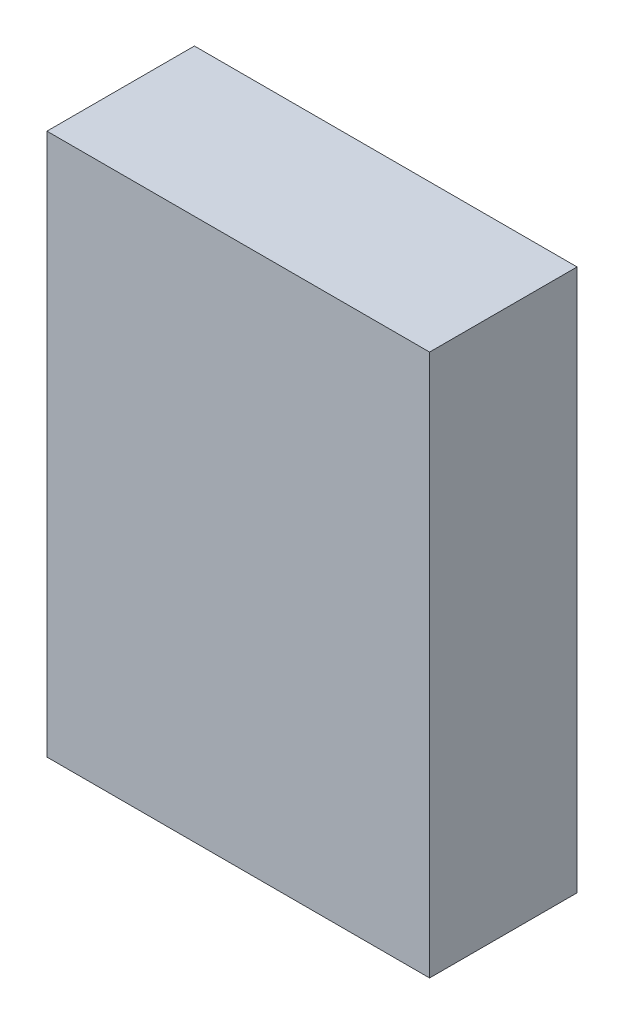
SolidWorks part; units mm, degrees
ref_plane "Plan de face" through (0, 0, 0) normal (0, 0, 1) x (1, 0, 0)
ref_plane "Plan de dessus" through (0, 0, 0) normal (0, 1, 0) x (1, 0, 0)
ref_plane "Plan de droite" through (0, 0, 0) normal (1, 0, 0) x (0, 0, -1)
sketch "Esquisse1" plane through (0, 0, 0) normal (0, 0, 1) x (1, 0, 0)
  line L1 (24, -34) -> (-24, -34)
  line L2 (24, -34) -> (24, 34)
  line L3 (24, 34) -> (-24, 34)
  line L4 (-24, -34) -> (-24, 34)
  line L5 (24, -34) -> (-24, 34) construction
  line L6 (24, 34) -> (-24, -34) construction
  point P0 (0, 0)
  dimension "D1" = 68
  dimension "D2" = 48
extrude "Boss.-Extru.1" add sketch "Esquisse1" along normal blind 18.5
sketch "Esquisse2" plane through (0, 0, 0) normal (0, 0, -1) x (-1, 0, 0)
  line L0 (24, 34) -> (24, -34) construction
  line L1 (18, 31) -> (10, 31)
  line L2 (18, 31) -> (18, 27)
  line L3 (18, 27) -> (10, 27)
  line L4 (10, 31) -> (10, 27)
  line L5 (18, 31) -> (10, 27) construction
  line L6 (18, 27) -> (10, 31) construction
  line L7 (-24, 34) -> (24, 34) construction
  point P0 (14, 29)
  dimension "D1" = 4
  dimension "D2" = 8
  dimension "D3" = 6
  dimension "D4" = 3
extrude "Boss.-Extru.2" add sketch "Esquisse2" along normal blind 2
